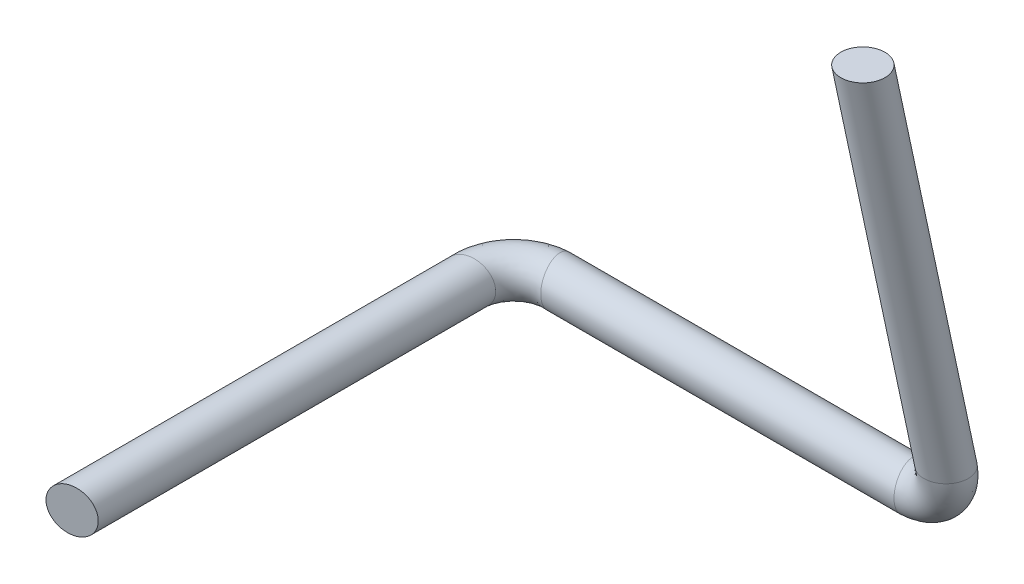
SolidWorks part; units mm, degrees
ref_plane "Plano frontal" through (0, 0, 0) normal (0, 0, 1) x (1, 0, 0)
ref_plane "Plano superior" through (0, 0, 0) normal (0, 1, 0) x (1, 0, 0)
ref_plane "Plano direito" through (0, 0, 0) normal (1, 0, 0) x (0, 0, -1)
sketch3d "3DSketch2"
  line L0 (0, 0, 0) -> (0.0381, -88.0088, -18.8064)
  line L1 (-9.9619, -97.7922, -20.897) -> (-89.9576, -97.7922, -20.897)
  line L2 (-99.9576, -97.7922, -10.897) -> (-99.9576, -97.7922, 79.103)
  arc A0 (0.0381, -88.0088, -18.8064) -> (-9.9619, -97.7922, -20.897) centre (-9.9619, -88.013, -18.8073) ccw
  arc A1 (-89.9576, -97.7922, -20.897) -> (-99.9576, -97.7922, -10.897) centre (-89.9576, -97.7922, -10.897) ccw
  point P7 (0.0424, -97.7922, -20.897)
  point P8 (-9.9619, -85.9233, -28.5865)
  point P11 (-99.9576, -97.7922, -20.897)
  point P12 (-89.9576, -87.7922, -10.897)
  dimension "D4" = 10
  dimension "D1" = 100
  dimension "D2" = 100
  dimension "D3" = 100
sketch "Esboço2" plane through (0, 0, 0) normal (0, 1, 0) x (1, 0, 0)
  circle A0 centre (0, 0) radius 5
  dimension "D1" = 10
sweep "Varredura1" add profiles "Esboço2" path "3DSketch2"
